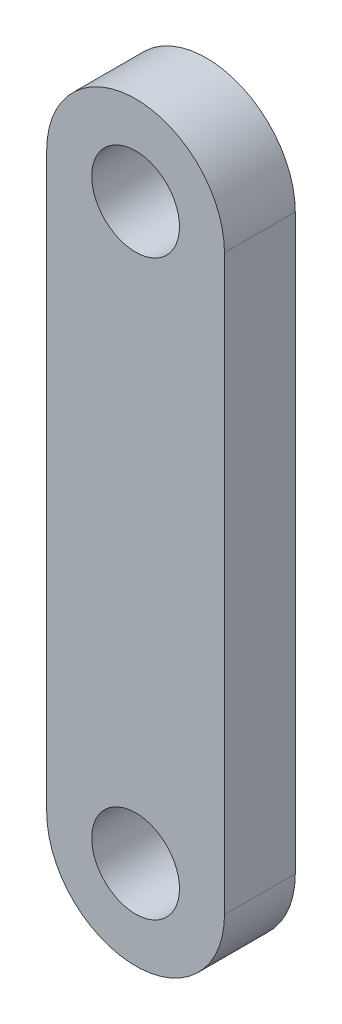
SolidWorks part; units mm, degrees
ref_plane "Front Plane" through (0, 0, 0) normal (0, 0, 1) x (1, 0, 0)
ref_plane "Top Plane" through (0, 0, 0) normal (0, 1, 0) x (1, 0, 0)
ref_plane "Right Plane" through (0, 0, 0) normal (1, 0, 0) x (0, 0, -1)
sketch "Sketch1" plane through (0, 0, 0) normal (0, 0, 1) x (1, 0, 0)
  line L0 (0, 38.075) -> (0, -13.36) construction
  line L1 (7.9756, 38.075) -> (7.9756, -13.36)
  line L2 (-7.9756, 38.075) -> (-7.9756, -13.36)
  arc A0 (7.9756, 38.075) -> (-7.9756, 38.075) centre (0, 38.075) ccw
  arc A1 (-7.9756, -13.36) -> (7.9756, -13.36) centre (0, -13.36) ccw
  circle A2 centre (0, 38.075) radius 3.937
  circle A3 centre (0, -13.36) radius 3.937
  point P3 (0, 12.3575)
  dimension "D1" = 7.874
  dimension "D2" = 7.874
  dimension "D3" = 51.435
  dimension "D4" = 15.9512
extrude "Boss-Extrude1" add sketch "Sketch1" along normal blind 6.35
